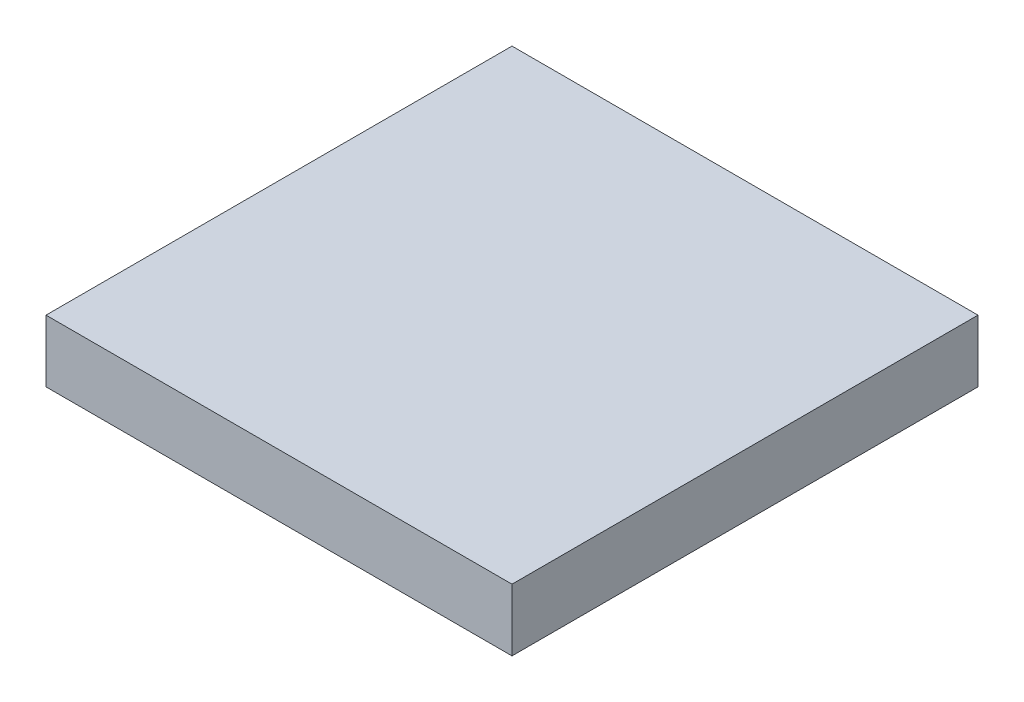
SolidWorks part; units mm, degrees
ref_plane "Front Plane" through (0, 0, 0) normal (0, 0, 1) x (1, 0, 0)
ref_plane "Top Plane" through (0, 0, 0) normal (0, 1, 0) x (1, 0, 0)
ref_plane "Right Plane" through (0, 0, 0) normal (1, 0, 0) x (0, 0, -1)
sketch "Sketch1" plane through (0, 0, 0) normal (0, 1, 0) x (1, 0, 0)
  line L1 (0, 0) -> (15, 0)
  line L2 (0, 0) -> (0, 15)
  line L3 (0, 15) -> (15, 15)
  line L4 (15, 0) -> (15, 15)
  dimension "D1" = 15
  dimension "D2" = 15
extrude "Boss-Extrude1" add sketch "Sketch1" along normal blind 2
